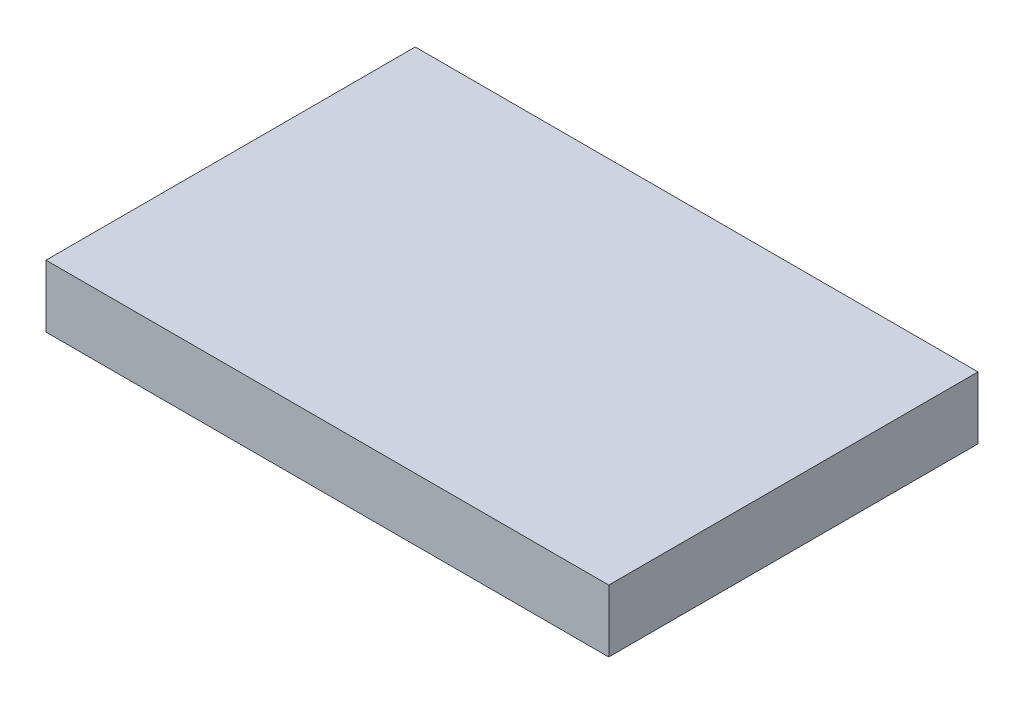
SolidWorks part; units mm, degrees
ref_plane "前视基准面" through (0, 0, 0) normal (0, 0, 1) x (1, 0, 0)
ref_plane "上视基准面" through (0, 0, 0) normal (0, 1, 0) x (1, 0, 0)
ref_plane "右视基准面" through (0, 0, 0) normal (1, 0, 0) x (0, 0, -1)
sketch "Sketch1" plane through (0, 0, 0) normal (0, 1, 0) x (1, 0, 0)
  line L1 (-40.64, -26.665) -> (40.64, -26.665)
  line L2 (-40.64, -26.665) -> (-40.64, 26.665)
  line L3 (-40.64, 26.665) -> (40.64, 26.665)
  line L4 (40.64, -26.665) -> (40.64, 26.665)
  line L5 (-40.64, -26.665) -> (40.64, 26.665) construction
  line L6 (-40.64, 26.665) -> (40.64, -26.665) construction
  point P0 (0, 0)
  dimension "D1" = 53.33
  dimension "D2" = 81.28
extrude "Boss-Extrude1" add sketch "Sketch1" along normal blind 9
